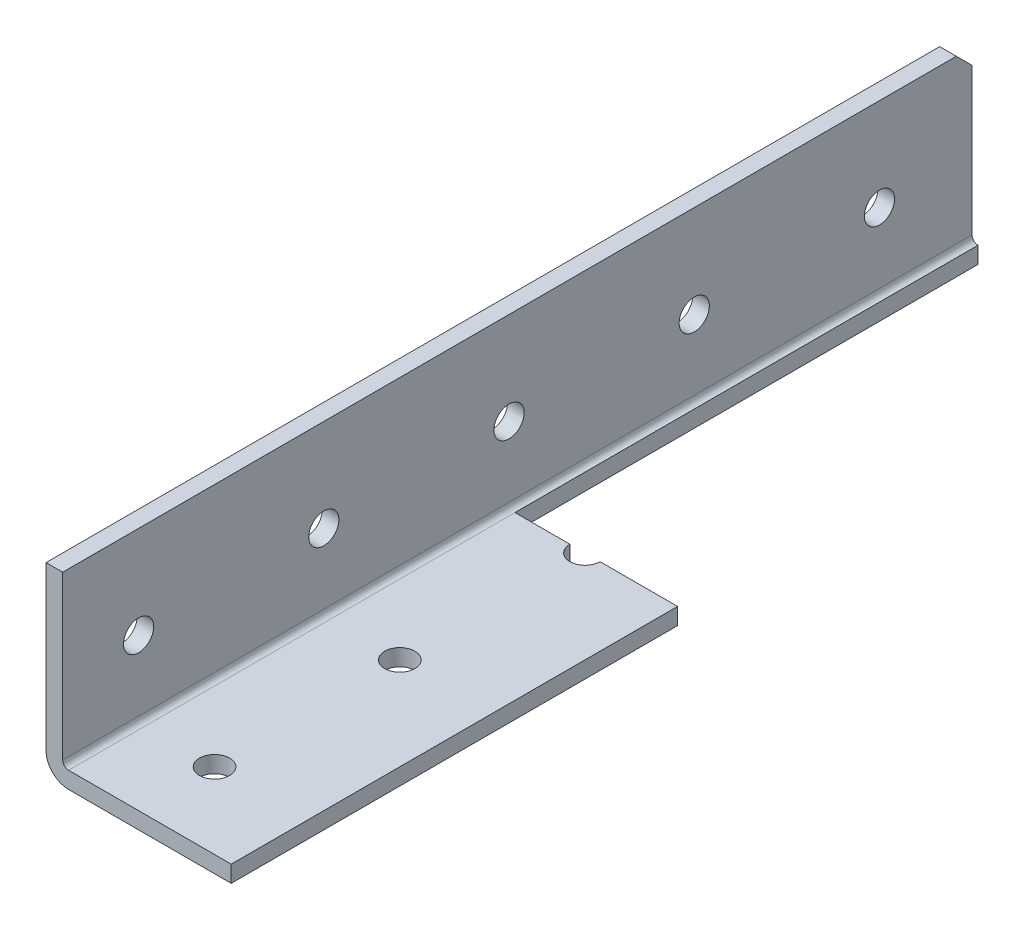
SolidWorks part; units mm, degrees
material "6061-T6 (SS)"
ref_plane "Front Plane" through (0, 0, 0) normal (0, 0, 1) x (1, 0, 0)
ref_plane "Top Plane" through (0, 0, 0) normal (0, 1, 0) x (1, 0, 0)
ref_plane "Right Plane" through (0, 0, 0) normal (1, 0, 0) x (0, 0, -1)
ref_plane "Plane1" through (0, 0, 0) normal (-1, 0, 0) x (0, -1, 0)
sketch "Sketch1" plane through (0, 0, 0) normal (-1, 0, 0) x (0, -1, 0)
  line L0 (0, 749.3) -> (-25.4, 749.3)
  line L1 (-25.4, 749.3) -> (-25.4, -749.3)
  line L2 (-25.4, -749.3) -> (0, -749.3)
  line L3 (0, -749.3) -> (0, 749.3)
extrude "Boss-Extrude1" add sketch "Sketch1" against normal blind 25.4
sketch "Sketch2" plane through (0, 0, -749.3) normal (0, 0, -1) x (-1, 0, 0)
  line L0 (-25.4, 2.286) -> (-2.286, 2.286)
  line L1 (-2.286, 2.286) -> (-2.286, 25.4)
  line L2 (-2.286, 25.4) -> (-25.4, 25.4)
  line L3 (-25.4, 25.4) -> (-25.4, 2.286)
extrude "Cut-Extrude1" cut sketch "Sketch2" against normal through all
hole_wizard "M3.5 Clearance Hole1" positions "Sketch4" profile "Sketch3" hole size "M3.5" standard "ANSI Metric"
sketch "Sketch4" plane through (0, 0, 0) normal (0, -1, 0) x (-1, 0, 0)
  point P0 (-12.7, 736.6)
  point P1 (-12.7, 711.2)
  point P2 (-12.7, 685.8)
  point P3 (-12.7, 660.4)
  point P4 (-12.7, 635)
  point P5 (-12.7, 609.6)
  point P6 (-12.7, 584.2)
  point P7 (-12.7, 558.8)
  point P8 (-12.7, 533.4)
  point P9 (-12.7, 508)
  point P10 (-12.7, 482.6)
  point P11 (-12.7, 457.2)
  point P12 (-12.7, 431.8)
  point P13 (-12.7, 406.4)
  point P14 (-12.7, 381)
  point P15 (-12.7, 355.6)
  point P16 (-12.7, 330.2)
  point P17 (-12.7, 304.8)
  point P18 (-12.7, 279.4)
  point P19 (-12.7, 254)
  point P20 (-12.7, 228.6)
  point P21 (-12.7, 203.2)
  point P22 (-12.7, 177.8)
  point P23 (-12.7, 152.4)
  point P24 (-12.7, 127)
  point P25 (-12.7, 101.6)
  point P26 (-12.7, 76.2)
  point P27 (-12.7, 50.8)
  point P28 (-12.7, 25.4)
  point P29 (-12.7, 0)
  point P30 (-12.7, -25.4)
  point P31 (-12.7, -50.8)
  point P32 (-12.7, -76.2)
  point P33 (-12.7, -101.6)
  point P34 (-12.7, -127)
  point P35 (-12.7, -152.4)
  point P36 (-12.7, -177.8)
  point P37 (-12.7, -203.2)
  point P38 (-12.7, -228.6)
  point P39 (-12.7, -254)
  point P40 (-12.7, -279.4)
  point P41 (-12.7, -304.8)
  point P42 (-12.7, -330.2)
  point P43 (-12.7, -355.6)
  point P44 (-12.7, -381)
  point P45 (-12.7, -406.4)
  point P46 (-12.7, -431.8)
  point P47 (-12.7, -457.2)
  point P48 (-12.7, -482.6)
  point P49 (-12.7, -508)
  point P50 (-12.7, -533.4)
  point P51 (-12.7, -558.8)
  point P52 (-12.7, -584.2)
  point P53 (-12.7, -609.6)
  point P54 (-12.7, -635)
  point P55 (-12.7, -660.4)
  point P56 (-12.7, -685.8)
  point P57 (-12.7, -711.2)
  point P58 (-12.7, -736.6)
sketch "Sketch3" plane through (12.7, 0, -736.6) normal (1, 0, 0) x (0, 0, -1)
  line L0 (0, 0) -> (0, 25.4)
  line L1 (0, 25.4) -> (2.0701, 25.4)
  line L2 (2.0701, 25.4) -> (2.0701, 0)
  line L5 (2.0701, 0) -> (0, 0)
  line L11 (0, -6.35) -> (0, 107.95) construction
  dimension "Thru Hole Dia." = 4.1402
  dimension "Thru Hole Depth" = 25.4
hole_wizard "M3.5 Clearance Hole2" positions "Sketch6" profile "Sketch5" hole size "M3.5" standard "ANSI Metric"
sketch "Sketch6" plane through (0, 0, 0) normal (-1, 0, 0) x (0, 0, 1)
  point P0 (711.2, 12.7)
  point P1 (736.6, 12.7)
  point P2 (685.8, 12.7)
  point P3 (660.4, 12.7)
  point P4 (635, 12.7)
  point P5 (609.6, 12.7)
  point P6 (584.2, 12.7)
  point P7 (558.8, 12.7)
  point P8 (533.4, 12.7)
  point P9 (508, 12.7)
  point P10 (482.6, 12.7)
  point P11 (457.2, 12.7)
  point P12 (431.8, 12.7)
  point P13 (406.4, 12.7)
  point P14 (381, 12.7)
  point P15 (355.6, 12.7)
  point P16 (330.2, 12.7)
  point P17 (304.8, 12.7)
  point P18 (279.4, 12.7)
  point P19 (254, 12.7)
  point P20 (228.6, 12.7)
  point P21 (203.2, 12.7)
  point P22 (177.8, 12.7)
  point P23 (152.4, 12.7)
  point P24 (127, 12.7)
  point P25 (101.6, 12.7)
  point P26 (76.2, 12.7)
  point P27 (50.8, 12.7)
  point P28 (25.4, 12.7)
  point P29 (0, 12.7)
  point P30 (-25.4, 12.7)
  point P31 (-50.8, 12.7)
  point P32 (-76.2, 12.7)
  point P33 (-101.6, 12.7)
  point P34 (-127, 12.7)
  point P35 (-152.4, 12.7)
  point P36 (-177.8, 12.7)
  point P37 (-203.2, 12.7)
  point P38 (-228.6, 12.7)
  point P39 (-254, 12.7)
  point P40 (-279.4, 12.7)
  point P41 (-304.8, 12.7)
  point P42 (-330.2, 12.7)
  point P43 (-355.6, 12.7)
  point P44 (-381, 12.7)
  point P45 (-406.4, 12.7)
  point P46 (-431.8, 12.7)
  point P47 (-457.2, 12.7)
  point P48 (-482.6, 12.7)
  point P49 (-508, 12.7)
  point P50 (-533.4, 12.7)
  point P51 (-558.8, 12.7)
  point P52 (-584.2, 12.7)
  point P53 (-609.6, 12.7)
  point P54 (-635, 12.7)
  point P55 (-660.4, 12.7)
  point P56 (-685.8, 12.7)
  point P57 (-711.2, 12.7)
  point P58 (-736.6, 12.7)
sketch "Sketch5" plane through (0, 12.7, 711.2) normal (0, 1, 0) x (0, 0, 1)
  line L0 (0, 0) -> (0, 25.4)
  line L1 (0, 25.4) -> (2.0701, 25.4)
  line L2 (2.0701, 25.4) -> (2.0701, 0)
  line L5 (2.0701, 0) -> (0, 0)
  line L11 (0, -6.35) -> (0, 107.95) construction
  dimension "Thru Hole Dia." = 4.1402
  dimension "Thru Hole Depth" = 25.4
chamfer "Chamfer1" distance 2.159 angle 45 4 edges at (25.4, 1.143, -749.3) (1.143, 25.4, -749.3) (1.143, 25.4, 749.3) (25.4, 1.143, 749.3)
fillet "Fillet1" radius 0.8128 1 edges at (2.286, 2.286, 0)
fillet "Fillet2" radius 3.0988 1 edges at (0, 0, 0)
sketch "Sketch8" plane through (0, 0, 749.3) normal (0, 0, 1) x (1, 0, 0)
  line L1 (-45.6555, -36.5704) -> (50.2275, -36.5704)
  line L2 (-45.6555, -36.5704) -> (-45.6555, 42.768)
  line L3 (-45.6555, 42.768) -> (50.2275, 42.768)
  line L4 (50.2275, -36.5704) -> (50.2275, 42.768)
  line L5 (-45.6555, -36.5704) -> (50.2275, 42.768) construction
  line L6 (-45.6555, 42.768) -> (50.2275, -36.5704) construction
  point P0 (2.286, 3.0988)
extrude "Cut-Extrude3" cut sketch "Sketch8" against normal blind 1371.6
sketch "Sketch11" plane through (0, 0, -622.3) normal (0, 0, 1) x (1, 0, 0)
  line L1 (-23.8761, -31.5895) -> (27.5864, -31.5895)
  line L2 (-23.8761, -31.5895) -> (-23.8761, 35.0872)
  line L3 (-23.8761, 35.0872) -> (27.5864, 35.0872)
  line L4 (27.5864, -31.5895) -> (27.5864, 35.0872)
  line L5 (-23.8761, -31.5895) -> (27.5864, 35.0872) construction
  line L6 (-23.8761, 35.0872) -> (27.5864, -31.5895) construction
  point P0 (1.8552, 1.7488)
extrude "Cut-Extrude6" cut sketch "Sketch11" against normal blind 2.286
sketch "Sketch12" plane through (0, 2.286, 0) normal (0, 1, 0) x (1, 0, 0)
  line L0 (3.0988, 749.3) -> (3.0988, 624.586) construction
  line L1 (3.0988, 685.8) -> (27.7333, 685.8)
  line L2 (3.0988, 685.8) -> (3.0988, 752.469)
  line L3 (3.0988, 752.469) -> (27.7333, 752.469)
  line L4 (27.7333, 685.8) -> (27.7333, 752.469)
extrude "Cut-Extrude7" cut sketch "Sketch12" against normal blind 2.54
